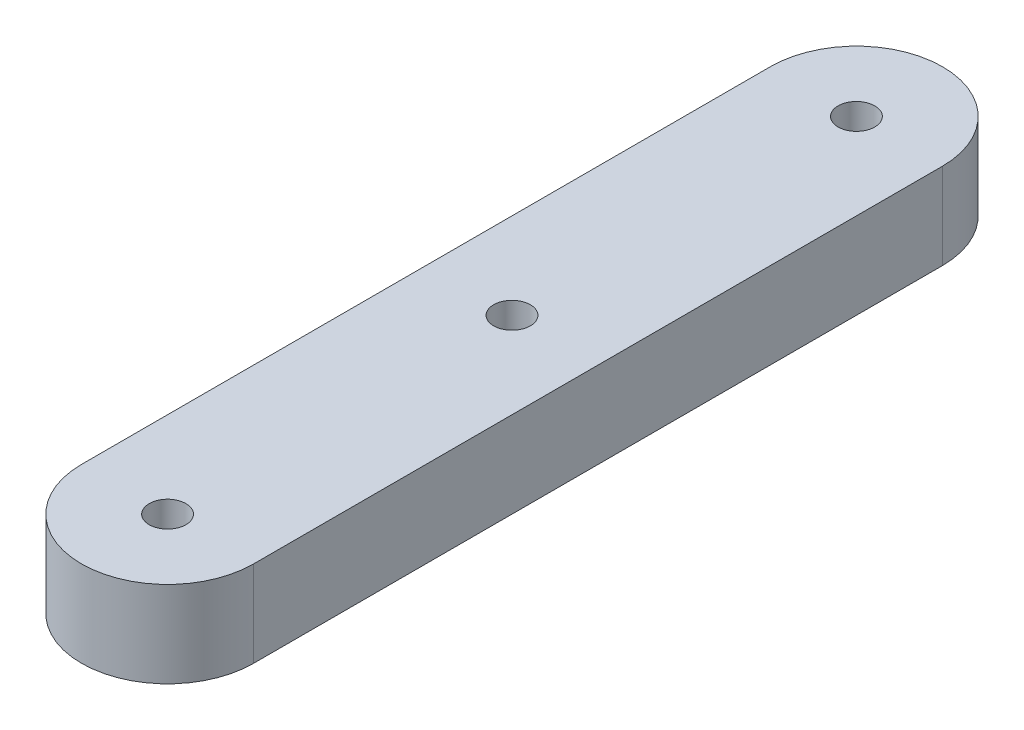
SolidWorks part; units mm, degrees
ref_plane "Front Plane" through (0, 0, 0) normal (0, 0, 1) x (1, 0, 0)
ref_plane "Top Plane" through (0, 0, 0) normal (0, 1, 0) x (1, 0, 0)
ref_plane "Right Plane" through (0, 0, 0) normal (1, 0, 0) x (0, 0, -1)
sketch "Sketch1" plane through (0, 0, 0) normal (0, 1, 0) x (1, 0, 0)
  line L0 (0, -25.4) -> (0, 25.4) construction
  line L1 (-6.35, -25.4) -> (-6.35, 25.4)
  line L2 (6.35, -25.4) -> (6.35, 25.4)
  arc A0 (-6.35, -25.4) -> (6.35, -25.4) centre (0, -25.4) ccw
  arc A1 (6.35, 25.4) -> (-6.35, 25.4) centre (0, 25.4) ccw
  point P2 (0, 0)
  dimension "D1" = 12.7
  dimension "D2" = 50.8
extrude "Boss-Extrude1" add sketch "Sketch1" along normal blind 6.35
hole_wizard "#6-32 Tapped Hole1" positions "Sketch2" profile "Sketch3" tap size "#6-32" standard "ANSI Inch" end condition through all
sketch "Sketch2" plane through (0, 6.35, 0) normal (0, 1, 0) x (1, 0, 0)
  point P0 (0, -25.4)
  point P3 (0, 25.4)
  point P5 (0, 0)
sketch "Sketch3" plane through (0, 6.35, 25.4) normal (1, 0, 0) x (0, 0, 1)
  line L0 (0, 0) -> (0, 6.35)
  line L1 (0, 6.35) -> (1.3525, 6.35)
  line L2 (1.3525, 6.35) -> (1.3525, 0)
  line L5 (1.3525, 0) -> (0, 0)
  line L11 (0, -6.35) -> (0, 107.95) construction
  dimension "Thru Tap Drill Dia." = 2.7051
  dimension "Thru Tap Drill Depth" = 6.35
cosmetic thread "Hole Thread1" parameters "D2"=3.5052
cosmetic thread "Hole Thread2" parameters "D2"=3.5052
cosmetic thread "Hole Thread3" parameters "D2"=3.5052
